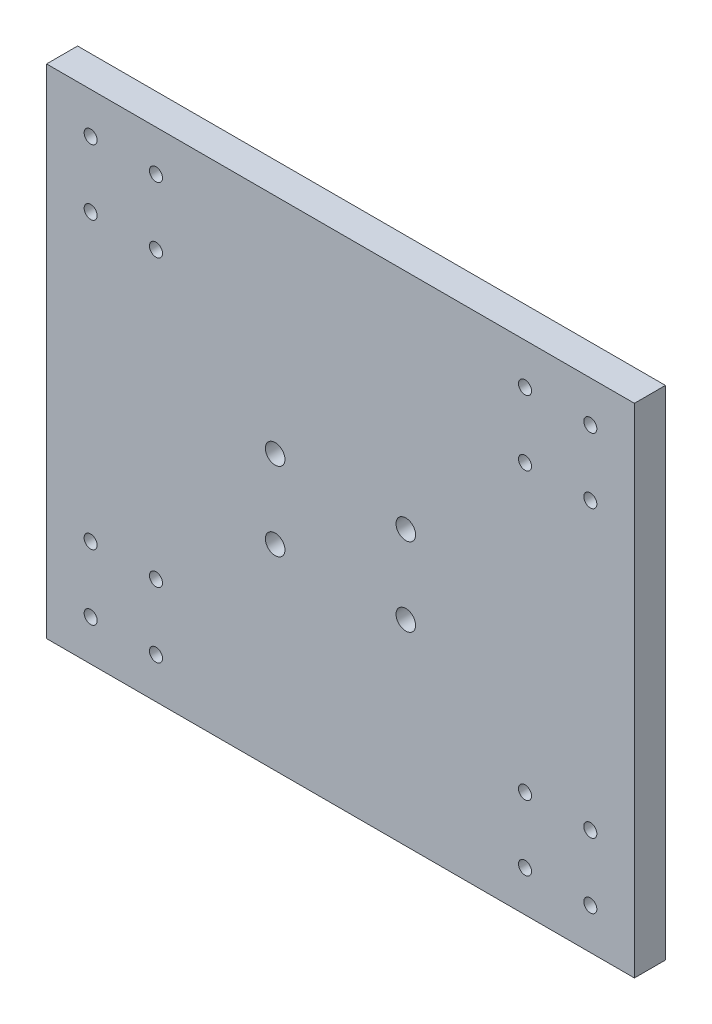
SolidWorks part; units mm, degrees
ref_plane "Front Plane" through (0, 0, 0) normal (0, 0, 1) x (1, 0, 0)
ref_plane "Top Plane" through (0, 0, 0) normal (0, 1, 0) x (1, 0, 0)
ref_plane "Right Plane" through (0, 0, 0) normal (1, 0, 0) x (0, 0, -1)
sketch "Sketch1" plane through (0, 0, 0) normal (0, 0, 1) x (1, 0, 0)
  line L1 (-90, -76.2) -> (90, -76.2)
  line L2 (-90, -76.2) -> (-90, 76.2)
  line L3 (-90, 76.2) -> (90, 76.2)
  line L4 (90, -76.2) -> (90, 76.2)
  line L5 (-90, -76.2) -> (90, 76.2) construction
  line L6 (-90, 76.2) -> (90, -76.2) construction
  point P0 (0, 0)
  dimension "D1" = 180
  dimension "D2" = 152.4
extrude "Boss-Extrude1" add sketch "Sketch1" along normal blind 9.5
sketch "Sketch2" plane through (0, 0, 9.5) normal (0, 0, 1) x (1, 0, 0)
  line L0 (0, 0) -> (0, 34.8482) construction
  line L1 (0, 0) -> (33.7173, 0) construction
  line L2 (-90, -76.2) -> (90, -76.2) construction
  line L3 (-76.5, -63.7) -> (-56.5, -63.7) construction
  line L4 (-76.5, -63.7) -> (-76.5, -43.7) construction
  line L5 (-76.5, -43.7) -> (-56.5, -43.7) construction
  line L6 (-56.5, -63.7) -> (-56.5, -43.7) construction
  line L7 (-76.5, -63.7) -> (-56.5, -43.7) construction
  line L8 (-76.5, -43.7) -> (-56.5, -63.7) construction
  line L9 (-90, 76.2) -> (-90, -76.2) construction
  line L10 (76.5, -43.7) -> (56.5, -63.7) construction
  line L11 (76.5, -63.7) -> (56.5, -43.7) construction
  line L12 (56.5, -63.7) -> (56.5, -43.7) construction
  line L13 (76.5, -43.7) -> (56.5, -43.7) construction
  line L14 (76.5, -63.7) -> (76.5, -43.7) construction
  line L15 (76.5, -63.7) -> (56.5, -63.7) construction
  line L16 (76.5, 63.7) -> (56.5, 63.7) construction
  line L17 (76.5, 63.7) -> (76.5, 43.7) construction
  line L18 (76.5, 43.7) -> (56.5, 43.7) construction
  line L19 (56.5, 63.7) -> (56.5, 43.7) construction
  line L20 (76.5, 63.7) -> (56.5, 43.7) construction
  line L21 (76.5, 43.7) -> (56.5, 63.7) construction
  line L22 (-76.5, 43.7) -> (-56.5, 63.7) construction
  line L23 (-76.5, 63.7) -> (-56.5, 43.7) construction
  line L24 (-56.5, 63.7) -> (-56.5, 43.7) construction
  line L25 (-76.5, 43.7) -> (-56.5, 43.7) construction
  line L26 (-76.5, 63.7) -> (-76.5, 43.7) construction
  line L27 (-76.5, 63.7) -> (-56.5, 63.7) construction
  line L29 (-20, -16.2) -> (20, -16.2) construction
  line L30 (-20, -16.2) -> (-20, 7.8) construction
  line L31 (-20, 7.8) -> (20, 7.8) construction
  line L32 (20, -16.2) -> (20, 7.8) construction
  line L33 (-20, -16.2) -> (20, 7.8) construction
  line L34 (-20, 7.8) -> (20, -16.2) construction
  circle A0 centre (-76.5, -43.7) radius 2
  circle A1 centre (-56.5, -43.7) radius 2
  circle A2 centre (-76.5, -63.7) radius 2
  circle A3 centre (-56.5, -63.7) radius 2
  circle A4 centre (56.5, -63.7) radius 2
  circle A5 centre (76.5, -63.7) radius 2
  circle A6 centre (56.5, -43.7) radius 2
  circle A7 centre (76.5, -43.7) radius 2
  circle A8 centre (76.5, 43.7) radius 2
  circle A9 centre (56.5, 43.7) radius 2
  circle A10 centre (76.5, 63.7) radius 2
  circle A11 centre (56.5, 63.7) radius 2
  circle A12 centre (-56.5, 63.7) radius 2
  circle A13 centre (-76.5, 63.7) radius 2
  circle A14 centre (-56.5, 43.7) radius 2
  circle A15 centre (-76.5, 43.7) radius 2
  circle A16 centre (-20, 7.8) radius 3
  circle A17 centre (20, 7.8) radius 3
  circle A18 centre (20, -16.2) radius 3
  circle A19 centre (-20, -16.2) radius 3
  point P1 (0, -4.2)
  point P3 (-66.5, -53.7)
  point P25 (66.5, -53.7)
  point P42 (66.5, 53.7)
  point P43 (-66.5, 53.7)
  point P54 (20, -4.2)
  dimension "D5" = 40
  dimension "D1" = 20
  dimension "D2" = 20
  dimension "D3" = 12.5
  dimension "D4" = 13.5
  dimension "D6" = 24
  dimension "D7" = 60
  dimension "D8" = 33.5
  dimension "D9" = 70
  dimension "D10" = 110
  dimension "D11" = 146.5
  dimension "D12" = 166.5
  dimension "D13" = 12.5
  dimension "D14" = 32.5
  dimension "D15" = 119.9
  dimension "D16" = 139.9
  dimension "D17" = 60
  dimension "D18" = 84
extrude "Cut-Extrude1" cut sketch "Sketch2" against normal blind 9.5
